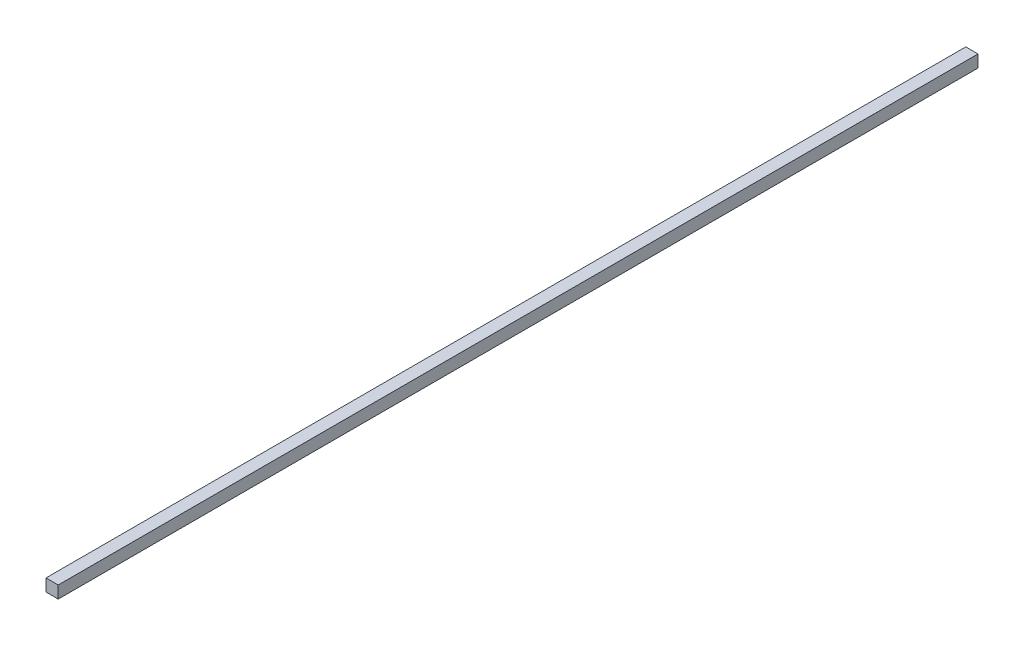
SolidWorks part; units mm, degrees
ref_plane "Front" through (0, 0, 0) normal (0, 0, 1) x (1, 0, 0)
ref_plane "Top" through (0, 0, 0) normal (0, 1, 0) x (1, 0, 0)
ref_plane "Right" through (0, 0, 0) normal (1, 0, 0) x (0, 0, -1)
sketch "Sketch1" plane through (0, 0, 0) normal (0, 0, 1) x (1, 0, 0)
  line L0 (-1.6891, 1.6891) -> (1.6891, 1.6891)
  line L5 (-1.5875, -1.5875) -> (1.5875, 1.5875) construction
  line L7 (1.6891, -1.6891) -> (1.6891, 1.6891)
  line L8 (-1.6891, -1.6891) -> (1.6891, -1.6891)
  line L9 (-1.6891, -1.6891) -> (-1.6891, 1.6891)
  point P0 (0, 0)
extrude "Boss-Extrude1" add sketch "Sketch1" along normal blind 254
